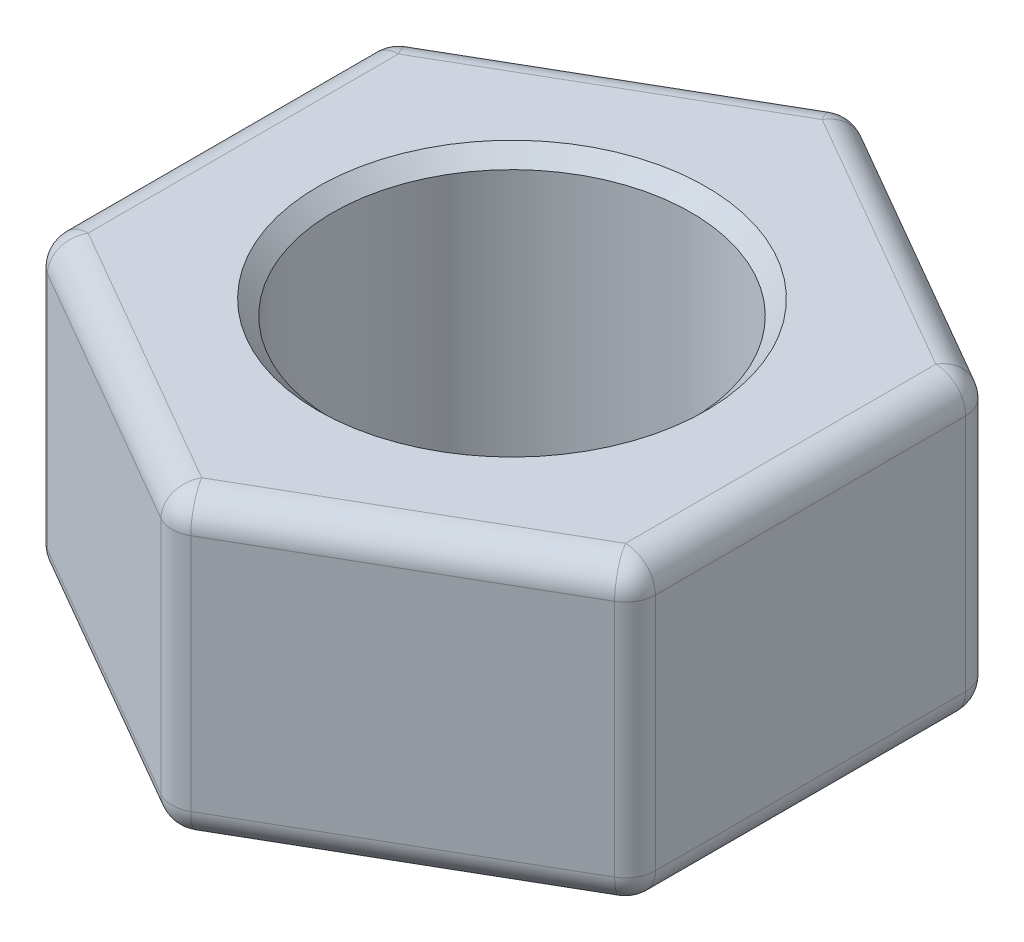
SolidWorks part; units mm, degrees
ref_plane "Front" through (0, 0, 0) normal (0, 0, 1) x (1, 0, 0)
ref_plane "Top" through (0, 0, 0) normal (0, 1, 0) x (1, 0, 0)
ref_plane "Right" through (0, 0, 0) normal (1, 0, 0) x (0, 0, -1)
sketch "Esquisse1" plane through (0, 0, 0) normal (0, 1, 0) x (1, 0, 0)
  line L0 (0, 0) -> (0, 5.7735) construction
  line L1 (0, 5.7735) -> (-5, 2.8868)
  line L2 (-5, 2.8868) -> (-5, -2.8868)
  line L3 (-5, -2.8868) -> (0, -5.7735)
  line L4 (0, -5.7735) -> (5, -2.8868)
  line L5 (5, -2.8868) -> (5, 2.8868)
  line L6 (5, 2.8868) -> (0, 5.7735)
  circle A0 centre (0, 0) radius 5 construction
  circle A1 centre (0, 0) radius 3
  dimension "D1" = 10
  dimension "D2" = 6
extrude "Boss.-Extru.1" add sketch "Esquisse1" along normal blind 5
fillet "Congé2" radius 0.5 18 edges at (-5, 5, 0) (-5, 0, 0) (-2.5, 5, -4.3301) (-5, 2.5, -2.8868) (-2.5, 0, -4.3301) (2.5, 5, -4.3301) (0, 2.5, -5.7735) (2.5, 0, -4.3301) (5, 5, 0) (5, 2.5, -2.8868) (5, 0, 0) (-5, 2.5, 2.8868) (-2.5, 5, 4.3301) (-2.5, 0, 4.3301) (0, 2.5, 5.7735) (2.5, 5, 4.3301) (5, 2.5, 2.8868) (2.5, 0, 4.3301)
chamfer "Chanfrein1" distance 0.25 angle 45 2 edges at (0, 0, 3) (0, 5, 3)
